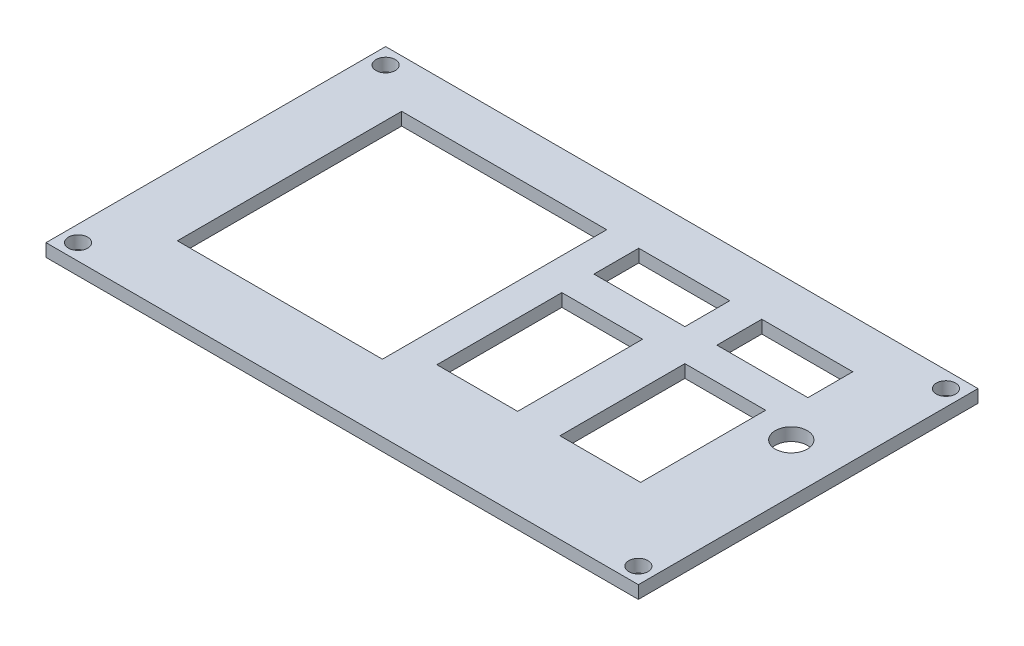
SolidWorks part; units mm, degrees
ref_plane "Front Plane" through (0, 0, 0) normal (0, 0, 1) x (1, 0, 0)
ref_plane "Top Plane" through (0, 0, 0) normal (0, 1, 0) x (1, 0, 0)
ref_plane "Right Plane" through (0, 0, 0) normal (1, 0, 0) x (0, 0, -1)
sketch "Sketch1" plane through (0, 0, 0) normal (0, 1, 0) x (1, 0, 0)
  line L1 (-46.22, 26.5) -> (46.22, 26.5)
  line L2 (-46.22, 26.5) -> (-46.22, -26.5)
  line L3 (-46.22, -26.5) -> (46.22, -26.5)
  line L4 (46.22, 26.5) -> (46.22, -26.5)
  line L5 (-46.22, 26.5) -> (46.22, -26.5) construction
  line L6 (-46.22, -26.5) -> (46.22, 26.5) construction
  point P0 (0, 0)
  dimension "D1" = 53
  dimension "D2" = 92.44
extrude "Boss-Extrude1" add sketch "Sketch1" along normal blind 2
sketch "Sketch2" plane through (0, 2, 0) normal (0, 1, 0) x (1, 0, 0)
  line L0 (-46.22, 26.5) -> (-46.22, -26.5) construction
  line L1 (46.22, 26.5) -> (-46.22, 26.5) construction
  line L2 (46.22, -26.5) -> (46.22, 26.5) construction
  line L3 (-46.22, -26.5) -> (46.22, -26.5) construction
  circle A0 centre (-43.72, 24) radius 1.5
  circle A1 centre (43.72, 24) radius 1.5
  circle A2 centre (43.72, -24) radius 1.5
  circle A3 centre (-43.72, -24) radius 1.5
  dimension "D1" = 3
  dimension "D2" = 3
  dimension "D3" = 3
  dimension "D4" = 3
  dimension "D5" = 2.5
  dimension "D6" = 2.5
  dimension "D7" = 2.5
  dimension "D8" = 2.5
  dimension "D9" = 2.5
  dimension "D10" = 2.5
  dimension "D11" = 2.5
  dimension "D12" = 2.5
extrude "Cut-Extrude1" cut sketch "Sketch2" against normal through all
sketch "Sketch3" plane through (0, 2, 0) normal (0, 1, 0) x (1, 0, 0)
  line L0 (-46.22, 0) -> (46.22, 0) construction
  line L1 (-46.22, 26.5) -> (-46.22, -26.5) construction
  line L2 (46.22, -26.5) -> (46.22, 26.5) construction
  line L4 (-36.22, 19) -> (-4.22, 19)
  line L5 (-36.22, 19) -> (-36.22, -16)
  line L6 (-36.22, -16) -> (-4.22, -16)
  line L7 (-4.22, 19) -> (-4.22, -16)
  line L8 (0.78, 19) -> (14.98, 19)
  line L9 (0.78, 19) -> (0.78, 12)
  line L10 (0.78, 12) -> (14.98, 12)
  line L11 (14.98, 19) -> (14.98, 12)
  line L12 (19.98, 19) -> (34.18, 19)
  line L13 (19.98, 19) -> (19.98, 12)
  line L14 (19.98, 12) -> (34.18, 12)
  line L15 (34.18, 19) -> (34.18, 12)
  line L16 (0.78, 7) -> (13.38, 7)
  line L17 (0.78, 7) -> (0.78, -12.5)
  line L18 (0.78, -12.5) -> (13.38, -12.5)
  line L19 (13.38, 7) -> (13.38, -12.5)
  line L20 (19.98, 7) -> (32.58, 7)
  line L21 (19.98, 7) -> (19.98, -12.5)
  line L22 (19.98, -12.5) -> (32.58, -12.5)
  line L23 (32.58, 7) -> (32.58, -12.5)
  circle A0 centre (38.58, 5) radius 2.5
  dimension "D17" = 5
  dimension "D1" = 35
  dimension "D2" = 32
  dimension "D3" = 16
  dimension "D4" = 10
  dimension "D5" = 5
  dimension "D6" = 5
  dimension "D7" = 14.2
  dimension "D8" = 14.2
  dimension "D9" = 7
  dimension "D10" = 7
  dimension "D11" = 5
  dimension "D12" = 5
  dimension "D13" = 12.6
  dimension "D14" = 19.5
  dimension "D15" = 12.6
  dimension "D16" = 19.5
  dimension "D18" = 6
  dimension "D19" = 5
extrude "Cut-Extrude2" cut sketch "Sketch3" against normal through all
